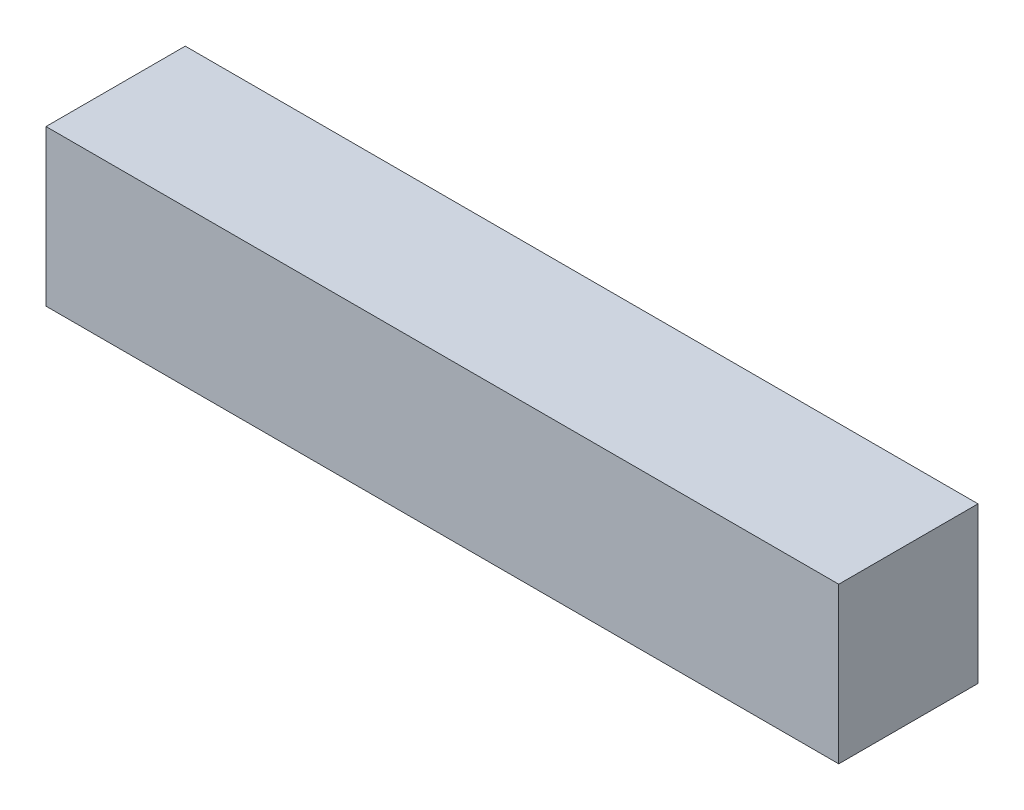
SolidWorks part; units mm, degrees
ref_plane "Front Plane" through (0, 0, 0) normal (0, 0, 1) x (1, 0, 0)
ref_plane "Top Plane" through (0, 0, 0) normal (0, 1, 0) x (1, 0, 0)
ref_plane "Right Plane" through (0, 0, 0) normal (1, 0, 0) x (0, 0, -1)
sketch "Sketch2" plane through (0, 0, 0) normal (0, 1, 0) x (1, 0, 0)
  line L0 (-50.2626, 2.7131) -> (-50.2626, -15.1869)
  line L5 (-50.2626, -15.1869) -> (51.6374, -15.1869)
  line L6 (51.6374, 2.7131) -> (51.6374, -15.1869)
  line L7 (-50.2626, 2.7131) -> (51.6374, 2.7131)
  line L8 (-51.2126, 3.6631) -> (-51.2126, -16.1369)
  line L9 (-51.2126, -16.1369) -> (52.5874, -16.1369)
  line L10 (52.5874, 3.6631) -> (52.5874, -16.1369)
  line L11 (-51.2126, 3.6631) -> (52.5874, 3.6631)
  dimension "D4" = 0.95
extrude "Boss-Extrude1" add sketch "Sketch2" along normal blind 20 contours L0 L5 L6 L7
